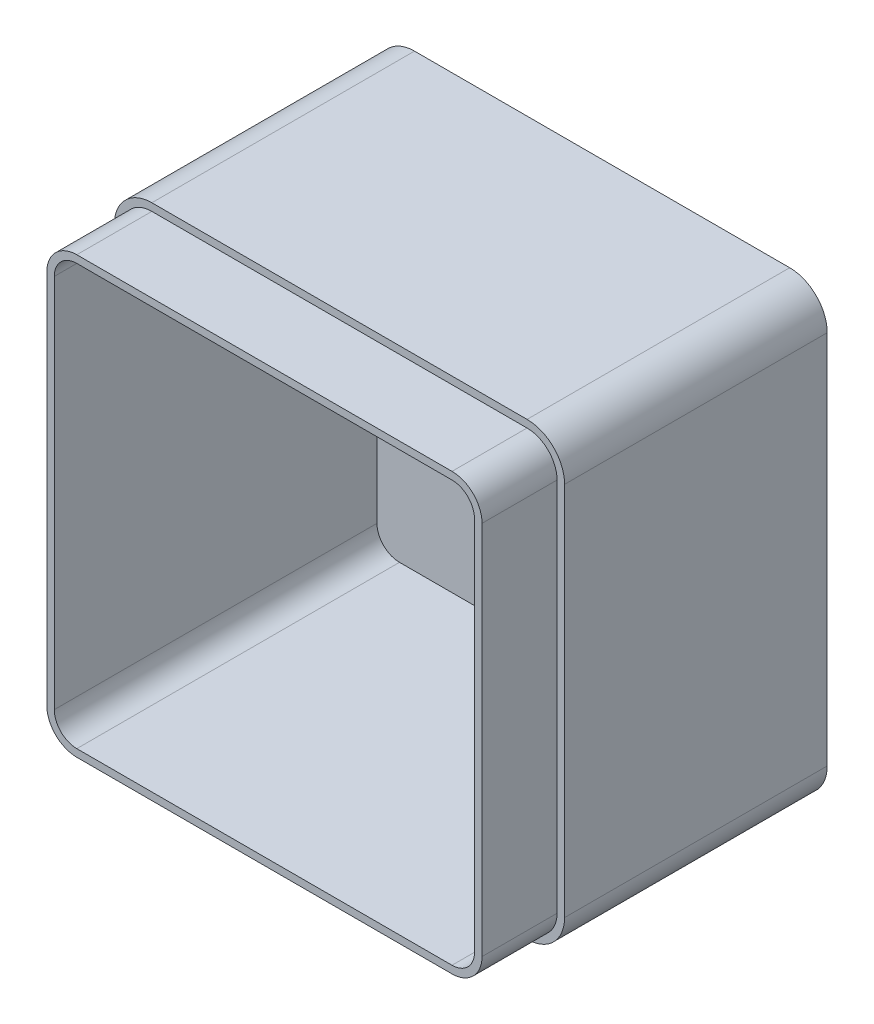
SolidWorks part; units mm, degrees
ref_plane "Front Plane" through (0, 0, 0) normal (0, 0, 1) x (1, 0, 0)
ref_plane "Top Plane" through (0, 0, 0) normal (0, 1, 0) x (1, 0, 0)
ref_plane "Right Plane" through (0, 0, 0) normal (1, 0, 0) x (0, 0, -1)
sketch "Sketch2" plane through (0, 0, 0) normal (0, 0, 1) x (1, 0, 0)
  line L1 (-56.5864, 41.3567) -> (63.4136, 41.3567)
  line L2 (-56.5864, 41.3567) -> (-56.5864, -78.6433)
  line L3 (-56.5864, -78.6433) -> (63.4136, -78.6433)
  line L4 (63.4136, 41.3567) -> (63.4136, -78.6433)
  dimension "D1" = 120
  dimension "D2" = 120
extrude "Boss-Extrude1" add sketch "Sketch2" along normal blind 90
fillet "Fillet1" radius 10 4 edges at (-56.5864, -78.6433, 45) (63.4136, -78.6433, 45) (63.4136, 41.3567, 45) (-56.5864, 41.3567, 45)
shell "Shell1" thickness 4
sketch "Sketch3" plane through (0, 0, 90) normal (0, 0, 1) x (1, 0, 0)
  line L0 (-54.5864, 31.3567) -> (-54.5864, -68.6433)
  line L1 (-46.5864, -76.6433) -> (53.4136, -76.6433)
  line L2 (61.4136, -68.6433) -> (61.4136, 31.3567)
  line L3 (53.4136, 39.3567) -> (-46.5864, 39.3567)
  line L4 (-56.5864, 31.3567) -> (-56.5864, -68.6433)
  line L5 (-46.5864, -78.6433) -> (53.4136, -78.6433)
  line L6 (63.4136, -68.6433) -> (63.4136, 31.3567)
  line L7 (53.4136, 41.3567) -> (-46.5864, 41.3567)
  line L8 (-56.5864, 31.3567) -> (-56.5864, -68.6433)
  line L9 (-46.5864, -78.6433) -> (53.4136, -78.6433)
  line L10 (63.4136, -68.6433) -> (63.4136, 31.3567)
  line L11 (53.4136, 41.3567) -> (-46.5864, 41.3567)
  arc A0 (-54.5864, -68.6433) -> (-46.5864, -76.6433) centre (-46.5864, -68.6433) ccw
  arc A1 (53.4136, -76.6433) -> (61.4136, -68.6433) centre (53.4136, -68.6433) ccw
  arc A2 (61.4136, 31.3567) -> (53.4136, 39.3567) centre (53.4136, 31.3567) ccw
  arc A3 (-46.5864, 39.3567) -> (-54.5864, 31.3567) centre (-46.5864, 31.3567) ccw
  arc A4 (-56.5864, -68.6433) -> (-46.5864, -78.6433) centre (-46.5864, -68.6433) ccw
  arc A5 (53.4136, -78.6433) -> (63.4136, -68.6433) centre (53.4136, -68.6433) ccw
  arc A6 (63.4136, 31.3567) -> (53.4136, 41.3567) centre (53.4136, 31.3567) ccw
  arc A7 (-46.5864, 41.3567) -> (-56.5864, 31.3567) centre (-46.5864, 31.3567) ccw
  arc A8 (-56.5864, -68.6433) -> (-46.5864, -78.6433) centre (-46.5864, -68.6433) ccw
  arc A9 (53.4136, -78.6433) -> (63.4136, -68.6433) centre (53.4136, -68.6433) ccw
  arc A10 (63.4136, 31.3567) -> (53.4136, 41.3567) centre (53.4136, 31.3567) ccw
  arc A11 (-46.5864, 41.3567) -> (-56.5864, 31.3567) centre (-46.5864, 31.3567) ccw
  dimension "D1" = 0
  dimension "D2" = 2
extrude "Cut-Extrude1" cut sketch "Sketch3" against normal blind 20
